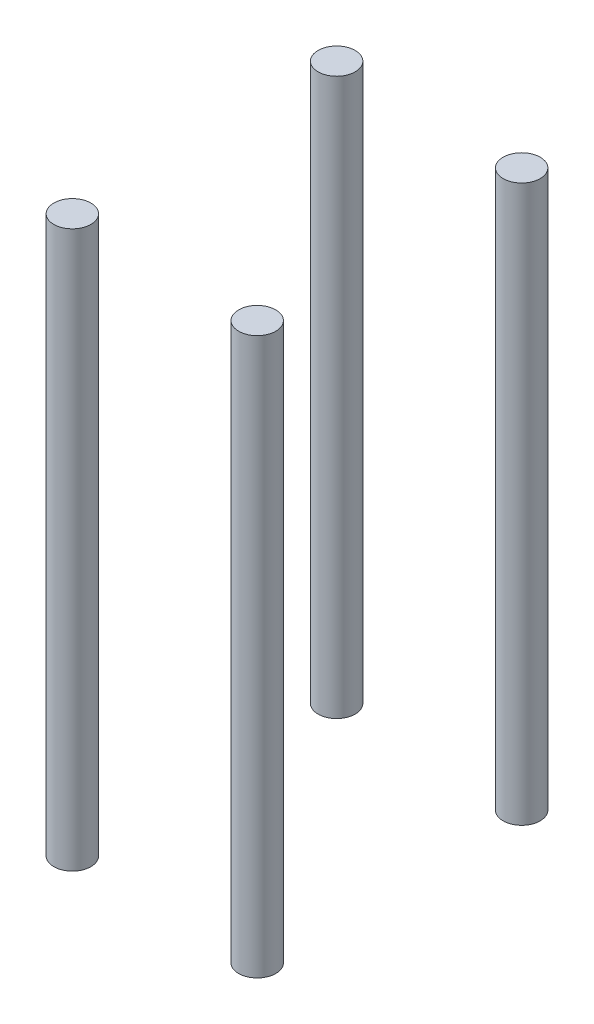
SolidWorks part; units mm, degrees
material "ASTM A36 Steel"
ref_plane "Front Plane" through (0, 0, 0) normal (0, 0, 1) x (1, 0, 0)
ref_plane "Top Plane" through (0, 0, 0) normal (0, 1, 0) x (1, 0, 0)
ref_plane "Right Plane" through (0, 0, 0) normal (1, 0, 0) x (0, 0, -1)
sketch "Sketch2" plane through (0, 0, 0) normal (0, 1, 0) x (1, 0, 0)
  line L0 (24.5753, 28.5189) -> (14.0753, 28.5189) construction
  line L1 (19.3253, 28.5189) -> (-20.5753, -28.5053) construction
  circle A0 centre (-0.625, 0.0068) radius 11 construction
  circle A1 centre (19.3253, 28.5189) radius 4
  circle A2 centre (-20.5753, 28.5053) radius 4
  circle A3 centre (19.3253, -28.5189) radius 4
  circle A4 centre (-20.5753, -28.5053) radius 4
extrude "Boss-Extrude1" add sketch "Sketch2" along normal blind 120
